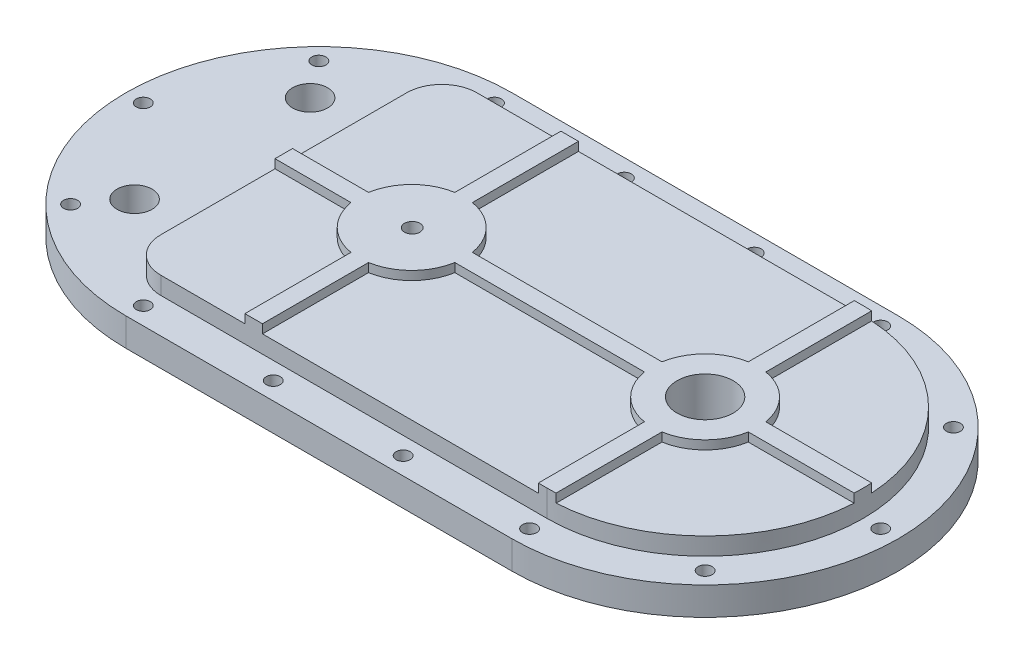
SolidWorks part; units mm, degrees
ref_plane "Front Plane" through (0, 0, 0) normal (0, 0, 1) x (1, 0, 0)
ref_plane "Top Plane" through (0, 0, 0) normal (0, 1, 0) x (1, 0, 0)
ref_plane "Right Plane" through (0, 0, 0) normal (1, 0, 0) x (0, 0, -1)
sketch "Sketch1" plane through (0, 0, 0) normal (0, 1, 0) x (1, 0, 0)
  line L0 (-110, 0) -> (110, 0) construction
  line L1 (-110, 110) -> (110, 110)
  line L2 (-110, -110) -> (110, -110)
  line L3 (-110, 0) -> (110, 0) construction
  line L4 (-110, 90) -> (110, 90)
  line L5 (-110, -90) -> (110, -90)
  line L6 (0, 110) -> (0, -110) construction
  arc A0 (-110, 110) -> (-110, -110) centre (-110, 0) ccw
  arc A1 (110, -110) -> (110, 110) centre (110, 0) ccw
  arc A2 (-110, 90) -> (-110, -90) centre (-110, 0) ccw
  arc A3 (110, -90) -> (110, 90) centre (110, 0) ccw
  point P2 (0, 0)
  point P10 (0, 0)
  dimension "D2" = 110
  dimension "D3" = 90
  dimension "D1" = 220
  dimension "D4" = 220
extrude "Boss-Extrude1" add sketch "Sketch1" along normal blind 16
hole_wizard "Ø8.0mm Dowel Hole1" positions "3DSketch12" profile "Sketch12" hole size "Ø8.0" standard "ANSI Metric" end condition through all
sketch3d "3DSketch12"
  line L0 (-110, 16, -110) -> (-110, 16, -90) construction
  point P0 (-110, 16, -100)
  point P9 (-110, 16, -100)
sketch "Sketch12" plane through (-110, 16, -100) normal (1, 0, 0) x (0, 0, 1)
  line L0 (0, 0) -> (0, 16)
  line L1 (0, 16) -> (4, 16)
  line L2 (4, 16) -> (4, 0)
  line L5 (4, 0) -> (0, 0)
  line L11 (0, -6.35) -> (0, 107.95) construction
  dimension "Thru Hole Dia." = 8
  dimension "Thru Hole Depth" = 16
pattern_circular "CirPattern2" count 5 over 180 about axis through (-110, 0, 0) along (0, 1, 0) of "Ø8.0mm Dowel Hole1"
mirror "Mirror2" about plane through (0, 0, 0) normal (1, 0, 0) of "CirPattern2", "Ø8.0mm Dowel Hole1"
pattern_linear "LPattern1" count 3 spacing 74 along (1, 0, 0) of "Ø8.0mm Dowel Hole1"
mirror "Mirror3" about plane through (0, 0, 0) normal (0, 0, 1) of "LPattern1"
sketch "Sketch13" plane through (0, 0, 0) normal (0, 1, 0) x (1, 0, 0)
  line L0 (-165, 71.239) -> (-165, -71.239) construction
  line L1 (-220, 0) -> (220, 0) construction
  line L2 (-110, -110) -> (110, -110)
  line L3 (110, 110) -> (-110, 110)
  line L4 (-110, -110) -> (110, -110)
  line L5 (110, 110) -> (-110, 110)
  arc A0 (-110, 90) -> (-110, -90) centre (-110, 0) ccw construction
  circle A1 centre (38, -100) radius 4
  arc A2 (-110, 110) -> (-110, -110) centre (-110, 0) ccw
  arc A3 (110, -110) -> (110, 110) centre (110, 0) ccw
  arc A4 (-110, 110) -> (-110, -110) centre (-110, 0) ccw
  arc A5 (110, -110) -> (110, 110) centre (110, 0) ccw
  circle A6 centre (38, -100) radius 4
  circle A7 centre (-110, 100) radius 4
  circle A8 centre (-110, 100) radius 4
  circle A9 centre (-180.7107, 70.7107) radius 4
  circle A10 centre (-180.7107, 70.7107) radius 4
  circle A11 centre (-210, 0) radius 4
  circle A12 centre (-210, 0) radius 4
  circle A13 centre (-180.7107, -70.7107) radius 4
  circle A14 centre (-180.7107, -70.7107) radius 4
  circle A15 centre (-110, -100) radius 4
  circle A16 centre (-110, -100) radius 4
  circle A17 centre (110, 100) radius 4
  circle A18 centre (110, 100) radius 4
  circle A19 centre (180.7107, 70.7107) radius 4
  circle A20 centre (180.7107, 70.7107) radius 4
  circle A21 centre (210, 0) radius 4
  circle A22 centre (210, 0) radius 4
  circle A23 centre (180.7107, -70.7107) radius 4
  circle A24 centre (180.7107, -70.7107) radius 4
  circle A25 centre (110, -100) radius 4
  circle A26 centre (110, -100) radius 4
  circle A27 centre (-36, 100) radius 4
  circle A28 centre (-36, 100) radius 4
  circle A29 centre (38, 100) radius 4
  circle A30 centre (38, 100) radius 4
  circle A31 centre (-36, -100) radius 4
  circle A32 centre (-36, -100) radius 4
  circle A33 centre (-165, -50) radius 10
  circle A34 centre (-165, 50) radius 10
  dimension "D18" = 20
  dimension "D16" = 45
  dimension "D17" = 50
  dimension "D1" = 0
  dimension "D2" = 0
  dimension "D3" = 0
  dimension "D4" = 0
  dimension "D5" = 0
  dimension "D6" = 0
  dimension "D7" = 0
  dimension "D8" = 0
  dimension "D9" = 0
  dimension "D10" = 0
  dimension "D11" = 0
  dimension "D12" = 0
  dimension "D13" = 0
  dimension "D14" = 0
  dimension "D15" = 0
extrude "Boss-Extrude2" add sketch "Sketch13" along normal blind 16
sketch "Sketch15" plane through (0, 0, 0) normal (0, 1, 0) x (1, 0, 0)
  line L0 (-110, -110) -> (110, -110) construction
  line L1 (110, 110) -> (-110, 110) construction
  line L2 (-110, -110) -> (110, -110)
  line L3 (110, 110) -> (-110, 110)
  line L5 (-110, -90) -> (110, -90)
  line L6 (-130, -70) -> (-130, 70)
  line L7 (-110, 90) -> (110, 90)
  line L8 (110, -90) -> (110, 90)
  arc A0 (-110, 110) -> (-110, -110) centre (-110, 0) ccw construction
  arc A1 (110, -110) -> (110, 110) centre (110, 0) ccw construction
  arc A2 (-110, 110) -> (-110, -110) centre (-110, 0) ccw
  arc A3 (110, -110) -> (110, 110) centre (110, 0) ccw
  arc A4 (-110, -90) -> (-130, -70) centre (-110, -70) cw
  arc A5 (-130, 70) -> (-110, 90) centre (-110, 70) cw
  arc A6 (110, 90) -> (110, -90) centre (110, 0) cw
  point P13 (-130, -90)
  point P16 (-130, 0)
  point P17 (-220, 0)
  dimension "D2" = 20
  dimension "D3" = 90
  dimension "D1" = 240
extrude "Boss-Extrude3" add sketch "Sketch15" along normal blind 26 contours A5 L6 A4 L5 L8 L7 | A6 L8
ref_plane "Plane1" through (0, 26, 0) normal (0, 1, 0) x (1, 0, 0)
sketch "Sketch16" plane through (0, 26, 0) normal (0, 1, 0) x (1, 0, 0)
  line L0 (-220, 0) -> (244.663, 0) construction
  line L1 (-130, 70) -> (-130, -70) construction
  line L2 (110, -90) -> (-110, -90) construction
  line L3 (110, 90) -> (-110, 90) construction
  line L4 (-130, 70) -> (-130, -70)
  line L5 (110, -90) -> (-110, -90)
  line L6 (110, 90) -> (-110, 90)
  line L7 (-224.28, 0) -> (110, 0) construction
  line L8 (26.43, 129.2067) -> (26.43, -129.2067) construction
  line L9 (-62.14, 90) -> (-62.14, -90)
  line L10 (-52.14, 90) -> (-52.14, -90)
  line L11 (-130, 5) -> (26.43, 5)
  line L12 (-130, -5) -> (26.43, -5)
  line L13 (115, 90) -> (115, -90)
  line L14 (105, 90) -> (105, -90)
  line L15 (26.43, 5) -> (199.861, 5)
  line L16 (26.43, -5) -> (199.861, -5)
  arc A0 (-110, 110) -> (-110, -110) centre (-110, 0) ccw construction
  arc A1 (-110, 90) -> (-130, 70) centre (-110, 70) ccw construction
  arc A2 (-130, -70) -> (-110, -90) centre (-110, -70) ccw construction
  arc A3 (110, -90) -> (110, 90) centre (110, 0) ccw construction
  arc A4 (-110, 90) -> (-130, 70) centre (-110, 70) ccw
  arc A5 (-130, -70) -> (-110, -90) centre (-110, -70) ccw
  arc A6 (110, -90) -> (110, 90) centre (110, 0) ccw
  circle A7 centre (-57.14, 0) radius 30
  circle A8 centre (110, 0) radius 30
  point P7 (-57.14, 0)
  point P8 (110, 0)
  point P12 (-130, 0)
  point P24 (-57.14, 0)
  point P26 (26.43, 0)
  dimension "D3" = 30
  dimension "D1" = 167.14
  dimension "D2" = 240
  dimension "D4" = 83.57
  dimension "D5" = 5
  dimension "D6" = 5
  dimension "D7" = 5
  dimension "D8" = 5
extrude "Boss-Extrude5" add sketch "Sketch16" along normal blind 5 contours L10 A7 L9 L11 | A7 L10 L6 L9 | L11 A7 L10 | L12 A7 L11 L10 | L9 L12 L10 L11 | L9 A7 L10 L12 | L11 A7 L12 L9 | L9 A7 L11 | L12 A7 L9 | L10 A7 L12 | L16 A8 L15 L11 A7 L12 | A7 L11 L4 L12 | A7 L9 L5 L10 | A8 L13 L15 | A8 L14 L15 L13 | A8 L15 L14 | A8 L16 L14 L15 | L14 L16 L13 L15 | A8 L15 L13 L16 | A8 L16 L13 | A8 L13 L16 L14 | A8 L14 L16 | L15 A8 L16 A6 | L14 A8 L13 A6 L6 | L13 A8 L14 L5 A6
hole_wizard "M10x1.25 Tapped Hole1" positions "3DSketch15" profile "Sketch18" tap size "M10x1.25" standard "ANSI Metric"
sketch3d "3DSketch15"
  line L0 (-130, 31, -5) -> (-130, 31, 5) construction
  point P0 (-56.8668, 31, 0)
  point P3 (-130, 31, 0)
  point P8 (-56.8668, 31, 0)
sketch "Sketch18" plane through (-56.8668, 31, 0) normal (1, 0, 0) x (0, 0, 1)
  line L0 (0, 0) -> (0, 31)
  line L1 (0, 31) -> (4.4, 31)
  line L2 (4.4, 31) -> (4.4, 0)
  line L5 (4.4, 0) -> (0, 0)
  line L11 (0, -6.35) -> (0, 107.95) construction
  dimension "Thru Tap Drill Dia." = 8.8
  dimension "Thru Tap Drill Depth" = 31
ref_plane "Plane2" through (0, 31, 0) normal (0, 1, 0) x (1, 0, 0)
sketch "Sketch19" plane through (0, 31, 0) normal (0, 1, 0) x (1, 0, 0)
  circle A0 centre (110, 0) radius 16
  dimension "D2" = 32
extrude "Cut-Extrude1" cut sketch "Sketch19" against normal through all
